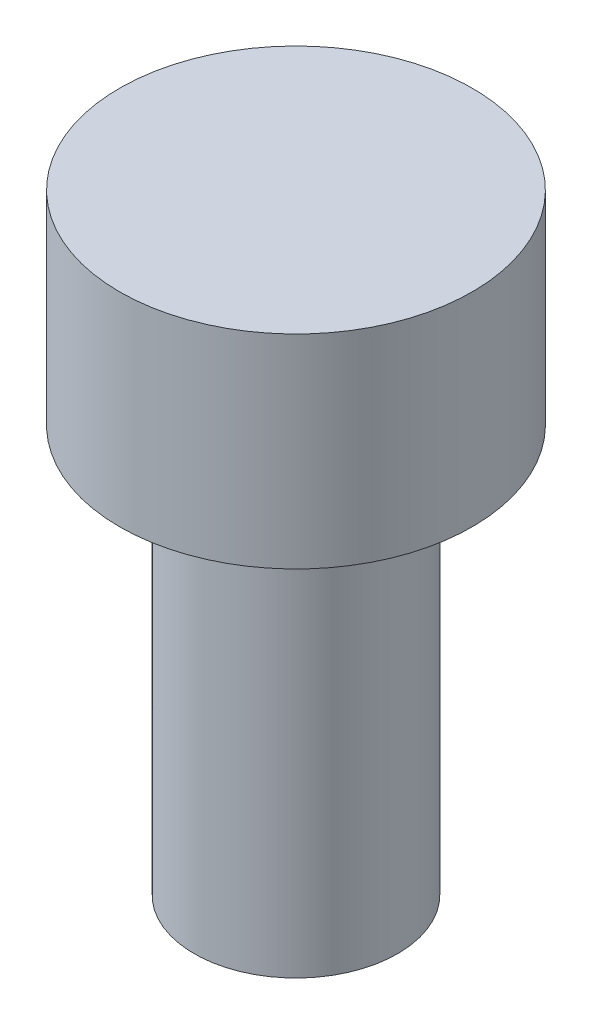
SolidWorks part; units mm, degrees
ref_plane "Front Plane" through (0, 0, 0) normal (0, 0, 1) x (1, 0, 0)
ref_plane "Top Plane" through (0, 0, 0) normal (0, 1, 0) x (1, 0, 0)
ref_plane "Right Plane" through (0, 0, 0) normal (1, 0, 0) x (0, 0, -1)
sketch "Sketch1" plane through (0, 0, 0) normal (0, 1, 0) x (1, 0, 0)
  circle A0 centre (0, 0) radius 2.6
  dimension "D1" = 5.2
extrude "Boss-Extrude1" add sketch "Sketch1" along normal blind 3
sketch "Sketch2" plane through (0, 0, 0) normal (0, -1, 0) x (1, 0, 0)
  circle A0 centre (0, 0) radius 1.5
  dimension "D1" = 3
extrude "Boss-Extrude2" add sketch "Sketch2" along normal blind 6
